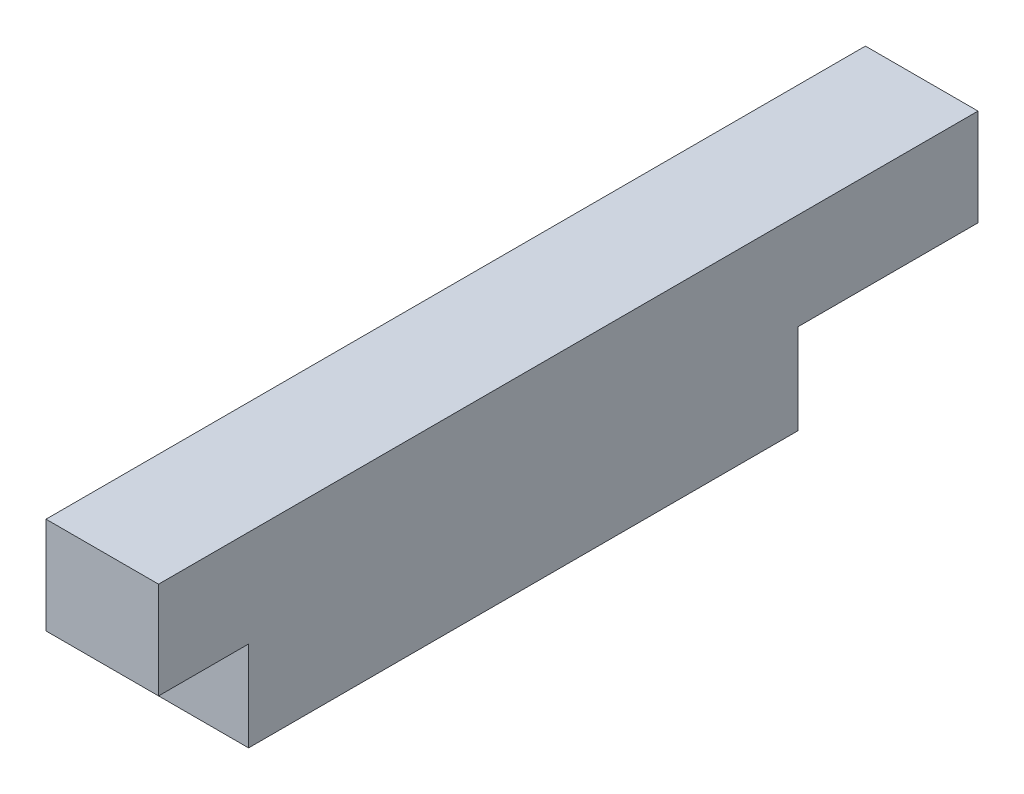
SolidWorks part; units mm, degrees
ref_plane "Front Plane" through (0, 0, 0) normal (0, 0, 1) x (1, 0, 0)
ref_plane "Top Plane" through (0, 0, 0) normal (0, 1, 0) x (1, 0, 0)
ref_plane "Right Plane" through (0, 0, 0) normal (1, 0, 0) x (0, 0, -1)
sketch "Sketch1" plane through (0, 0, 0) normal (1, 0, 0) x (0, 0, -1)
  line L0 (0, 4) -> (0, 8.3)
  line L1 (0, 8.3) -> (36.4, 8.3)
  line L2 (36.4, 8.3) -> (36.4, 4)
  line L3 (36.4, 4) -> (28.4, 4)
  line L4 (28.4, 4) -> (28.4, 0)
  line L5 (28.4, 0) -> (4, 0)
  line L6 (4, 0) -> (4, 4)
  line L7 (4, 4) -> (0, 4)
  dimension "D1" = 4
  dimension "D2" = 8
  dimension "D3" = 8.3
  dimension "D4" = 36.4
  dimension "D5" = 4
extrude "Boss-Extrude1" add sketch "Sketch1" along normal blind 5
hole_wizard "Tap Drill for M2x0.4 Tap1" positions "Sketch3" profile "Sketch2" hole size "M2x0.4" standard "ANSI Metric"
sketch "Sketch3" plane through (0, 0, 0) normal (0, -1, 0) x (-1, 0, 0)
  line L0 (-5, 36.4) -> (0, 36.4) construction
  line L1 (-5, 0) -> (0, 0) construction
  line L2 (0, 4) -> (0, 28.4) construction
  point P0 (-2.5, 9)
  point P2 (-2.5, 23.4)
  dimension "D1" = 13
  dimension "D2" = 9
  dimension "D3" = 2.5
sketch "Sketch2" plane through (2.5, 0, -9) normal (1, 0, 0) x (0, 0, -1)
  line L0 (0, 0) -> (0, 5)
  line L1 (0, 5) -> (0.8, 5)
  line L2 (0.8, 5) -> (0.8, 0)
  line L5 (0.8, 0) -> (0, 0)
  line L10 (0, 5) -> (-0.8, 5) construction
  line L11 (0, -6.35) -> (0, 107.95) construction
  dimension "Hole Dia." = 1.6
  dimension "Hole Depth" = 5
  dimension "Drill Angle" = 180
